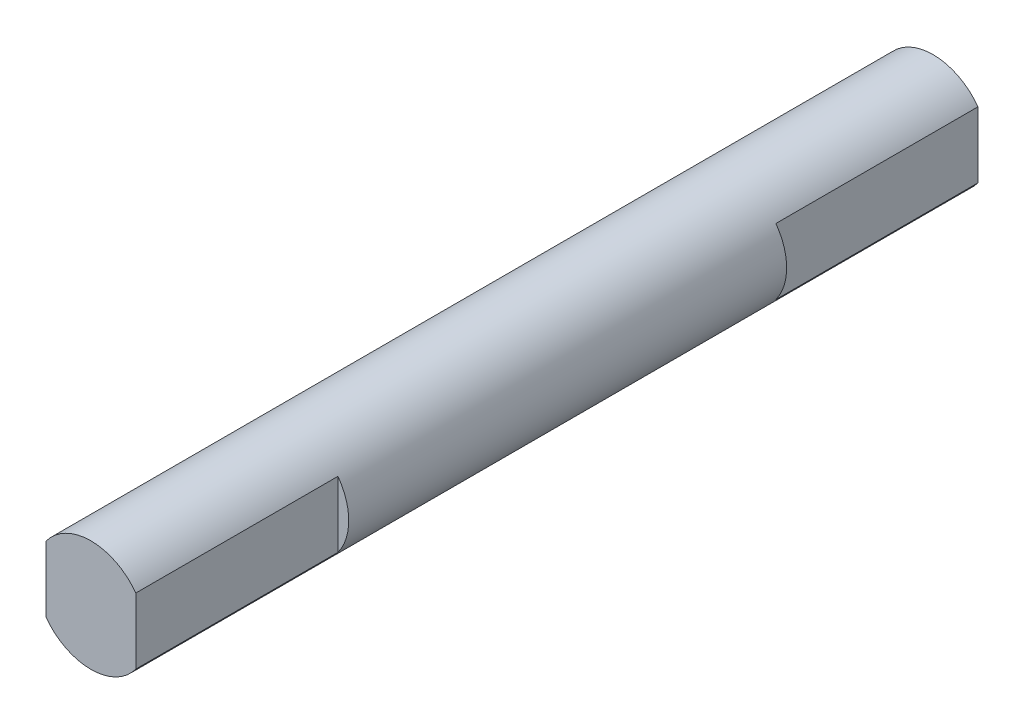
SolidWorks part; units mm, degrees
ref_plane "Front Plane" through (0, 0, 0) normal (0, 0, 1) x (1, 0, 0)
ref_plane "Top Plane" through (0, 0, 0) normal (0, 1, 0) x (1, 0, 0)
ref_plane "Right Plane" through (0, 0, 0) normal (1, 0, 0) x (0, 0, -1)
sketch "Sketch1" plane through (0, 0, 0) normal (0, 0, 1) x (1, 0, 0)
  circle A0 centre (0, 0) radius 2.48
  dimension "D1" = 4.96
extrude "Boss-Extrude1" add sketch "Sketch1" along normal blind 11 and the other way blind 5
sketch "Sketch2" plane through (0, 0, 11) normal (0, 0, 1) x (1, 0, 0)
  circle A1 centre (0, 0) radius 2.48
  circle A2 centre (0, 0) radius 2.48
  dimension "D1" = 0
extrude "Boss-Extrude2" add sketch "Sketch2" along normal blind 2
sketch "Sketch3" plane through (0, 0, 13) normal (0, 0, 1) x (1, 0, 0)
  line L2 (-2, 1.4664) -> (-2, -1.4664)
  line L4 (2, 1.4664) -> (2, -1.4664)
  line L5 (-2, 1.4664) -> (2, -1.4664) construction
  line L6 (-2, -1.4664) -> (2, 1.4664) construction
  circle A1 centre (0, 0) radius 2.48
  circle A2 centre (0, 0) radius 2.48
  circle M3 centre (0, 0) radius 2.48
  dimension "D2" = 4
  dimension "D1" = 0
extrude "Boss-Extrude3" add sketch "Sketch3" along normal blind 9 contours L4 L2 M3
sketch "Sketch4" plane through (0, 0, -5) normal (0, 0, -1) x (-1, 0, 0)
  circle A1 centre (0, 0) radius 2.48
  circle A2 centre (0, 0) radius 2.48
  dimension "D1" = 0
extrude "Boss-Extrude4" add sketch "Sketch4" along normal blind 1.5
sketch "Sketch5" plane through (0, 0, -6.5) normal (0, 0, -1) x (-1, 0, 0)
  line L2 (-2, 1.4664) -> (-2, -1.4664)
  line L4 (2, 1.4664) -> (2, -1.4664)
  line L5 (-2, 1.4664) -> (2, -1.4664) construction
  line L6 (-2, -1.4664) -> (2, 1.4664) construction
  circle A0 centre (0, 0) radius 2.48 construction
  circle A1 centre (0, 0) radius 2.48 construction
  circle A2 centre (0, 0) radius 2.48
  point P0 (0, 0)
  circle M2 centre (0, 0) radius 2.48
  dimension "D1" = 4
extrude "Boss-Extrude5" add sketch "Sketch5" along normal blind 9 contours L4 L2 M2
